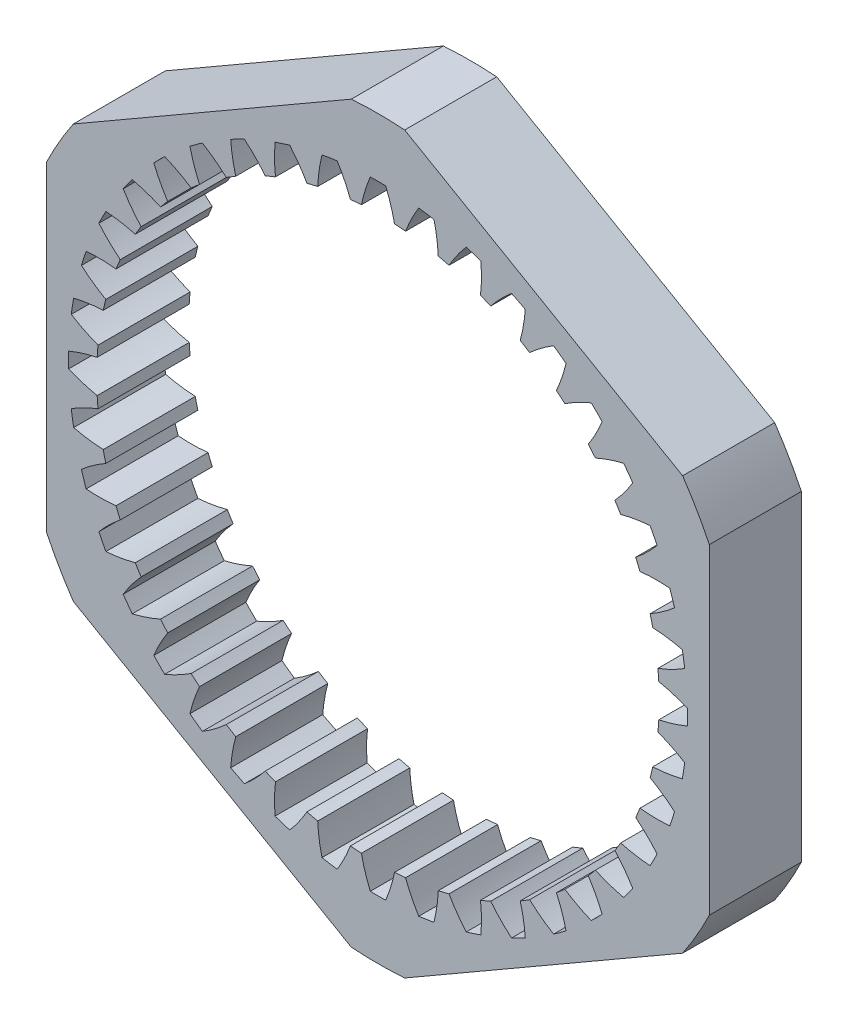
SolidWorks part; units mm, degrees
material "AISI 4130 Steel, annealed at 865C"
ref_plane "Front Plane" through (0, 0, 0) normal (0, 0, 1) x (1, 0, 0)
ref_plane "Top Plane" through (0, 0, 0) normal (0, 1, 0) x (1, 0, 0)
ref_plane "Right Plane" through (0, 0, 0) normal (1, 0, 0) x (0, 0, -1)
ref_plane "Plane1" through (0, 0, -7.9375) normal (0, 0, -1) x (-1, 0, 0)
sketch "Sketch1" plane through (0, 0, -7.9375) normal (0, 0, -1) x (-1, 0, 0)
  line L0 (-28.575, 13.8395) -> (-28.575, -13.8395)
  line L1 (-26.2729, -17.8269) -> (-2.3021, -31.6664)
  line L2 (2.3021, -31.6664) -> (26.2729, -17.8269)
  line L3 (28.575, -13.8395) -> (28.575, 13.8395)
  line L4 (26.2729, 17.8269) -> (2.3021, 31.6664)
  line L5 (-2.3021, 31.6664) -> (-26.2729, 17.8269)
  arc A0 (-26.2729, 17.8269) -> (-28.575, 13.8395) centre (0, 0) ccw
  arc A1 (-28.575, -13.8395) -> (-26.2729, -17.8269) centre (0, 0) ccw
  arc A2 (-2.3021, -31.6664) -> (2.3021, -31.6664) centre (0, 0) ccw
  arc A3 (26.2729, -17.8269) -> (28.575, -13.8395) centre (0, 0) ccw
  arc A4 (28.575, 13.8395) -> (26.2729, 17.8269) centre (0, 0) ccw
  arc A5 (2.3021, 31.6664) -> (-2.3021, 31.6664) centre (0, 0) ccw
  arc A6 (8.841, -22.5885) -> (8.8744, -25.1637) centre (-4.34, -24.0476) cw
  arc A7 (8.8744, -25.1637) -> (7.6113, -25.5741) centre (0, 0) cw
  arc A8 (7.6113, -25.5741) -> (6.1247, -23.4711) centre (17.6459, -16.9039) cw
  arc A9 (6.1247, -23.4711) -> (5.1985, -23.6934) centre (0, 0) cw
  arc A10 (5.1985, -23.6934) -> (4.8287, -26.2421) centre (-8.0484, -23.0726) cw
  arc A11 (4.8287, -26.2421) -> (3.5169, -26.4499) centre (0, 0) cw
  arc A12 (3.5169, -26.4499) -> (2.3776, -24.1402) centre (14.7843, -19.4562) cw
  arc A13 (2.3776, -24.1402) -> (1.428, -24.2149) centre (0, 0) cw
  arc A14 (1.428, -24.2149) -> (0.6641, -26.6744) centre (-11.5587, -21.5295) cw
  arc A15 (0.6641, -26.6744) -> (-0.6641, -26.6744) centre (0, 0) cw
  arc A16 (-0.6641, -26.6744) -> (-1.428, -24.2149) centre (11.5587, -21.5295) cw
  arc A17 (-1.428, -24.2149) -> (-2.3776, -24.1402) centre (0, 0) cw
  arc A18 (-2.3776, -24.1402) -> (-3.5169, -26.4499) centre (-14.7843, -19.4562) cw
  arc A19 (-3.5169, -26.4499) -> (-4.8287, -26.2421) centre (0, 0) cw
  arc A20 (-4.8287, -26.2421) -> (-5.1985, -23.6934) centre (8.0484, -23.0726) cw
  arc A21 (-5.1985, -23.6934) -> (-6.1247, -23.4711) centre (0, 0) cw
  arc A22 (-6.1247, -23.4711) -> (-7.6113, -25.5741) centre (-17.6459, -16.9039) cw
  arc A23 (-7.6113, -25.5741) -> (-8.8744, -25.1637) centre (0, 0) cw
  arc A24 (-8.8744, -25.1637) -> (-8.841, -22.5885) centre (4.34, -24.0476) cw
  arc A25 (-8.841, -22.5885) -> (-9.721, -22.224) centre (0, 0) cw
  arc A26 (-9.721, -22.224) -> (-11.5183, -24.0686) centre (-20.073, -13.9353) cw
  arc A27 (-11.5183, -24.0686) -> (-12.7016, -23.4656) centre (0, 0) cw
  arc A28 (-12.7016, -23.4656) -> (-12.2657, -20.9273) centre (0.5247, -24.4304) cw
  arc A29 (-12.2657, -20.9273) -> (-13.0779, -20.4297) centre (0, 0) cw
  arc A30 (-13.0779, -20.4297) -> (-15.1416, -21.9704) centre (-22.0059, -10.6237) cw
  arc A31 (-15.1416, -21.9704) -> (-16.2161, -21.1897) centre (0, 0) cw
  arc A32 (-16.2161, -21.1897) -> (-15.3885, -18.7509) centre (-3.3035, -24.2117) cw
  arc A33 (-15.3885, -18.7509) -> (-16.1128, -18.1323) centre (0, 0) cw
  arc A34 (-16.1128, -18.1323) -> (-18.3921, -19.3312) centre (-23.3969, -7.0504) cw
  arc A35 (-18.3921, -19.3312) -> (-19.3312, -18.3921) centre (0, 0) cw
  arc A36 (-19.3312, -18.3921) -> (-18.1323, -16.1128) centre (-7.0504, -23.3969) cw
  arc A37 (-18.1323, -16.1128) -> (-18.7509, -15.3885) centre (0, 0) cw
  arc A38 (-18.7509, -15.3885) -> (-21.1897, -16.2161) centre (-24.2117, -3.3035) cw
  arc A39 (-21.1897, -16.2161) -> (-21.9704, -15.1416) centre (0, 0) cw
  arc A40 (-21.9704, -15.1416) -> (-20.4297, -13.0779) centre (-10.6237, -22.0059) cw
  arc A41 (-20.4297, -13.0779) -> (-20.9273, -12.2657) centre (0, 0) cw
  arc A42 (-20.9273, -12.2657) -> (-23.4656, -12.7016) centre (-24.4304, 0.5247) cw
  arc A43 (-23.4656, -12.7016) -> (-24.0686, -11.5183) centre (0, 0) cw
  arc A44 (-24.0686, -11.5183) -> (-22.224, -9.721) centre (-13.9353, -20.073) cw
  arc A45 (-22.224, -9.721) -> (-22.5885, -8.841) centre (0, 0) cw
  arc A46 (-22.5885, -8.841) -> (-25.1637, -8.8744) centre (-24.0476, 4.34) cw
  arc A47 (-25.1637, -8.8744) -> (-25.5741, -7.6113) centre (0, 0) cw
  arc A48 (-25.5741, -7.6113) -> (-23.4711, -6.1247) centre (-16.9039, -17.6459) cw
  arc A49 (-23.4711, -6.1247) -> (-23.6934, -5.1985) centre (0, 0) cw
  arc A50 (-23.6934, -5.1985) -> (-26.2421, -4.8287) centre (-23.0726, 8.0484) cw
  arc A51 (-26.2421, -4.8287) -> (-26.4499, -3.5169) centre (0, 0) cw
  arc A52 (-26.4499, -3.5169) -> (-24.1402, -2.3776) centre (-19.4562, -14.7843) cw
  arc A53 (-24.1402, -2.3776) -> (-24.2149, -1.428) centre (0, 0) cw
  arc A54 (-24.2149, -1.428) -> (-26.6744, -0.6641) centre (-21.5295, 11.5587) cw
  arc A55 (-26.6744, -0.6641) -> (-26.6744, 0.6641) centre (0, 0) cw
  arc A56 (-26.6744, 0.6641) -> (-24.2149, 1.428) centre (-21.5295, -11.5587) cw
  arc A57 (-24.2149, 1.428) -> (-24.1402, 2.3776) centre (0, 0) cw
  arc A58 (-24.1402, 2.3776) -> (-26.4499, 3.5169) centre (-19.4562, 14.7843) cw
  arc A59 (-26.4499, 3.5169) -> (-26.2421, 4.8287) centre (0, 0) cw
  arc A60 (-26.2421, 4.8287) -> (-23.6934, 5.1985) centre (-23.0726, -8.0484) cw
  arc A61 (-23.6934, 5.1985) -> (-23.4711, 6.1247) centre (0, 0) cw
  arc A62 (-23.4711, 6.1247) -> (-25.5741, 7.6113) centre (-16.9039, 17.6459) cw
  arc A63 (-25.5741, 7.6113) -> (-25.1637, 8.8744) centre (0, 0) cw
  arc A64 (-25.1637, 8.8744) -> (-22.5885, 8.841) centre (-24.0476, -4.34) cw
  arc A65 (-22.5885, 8.841) -> (-22.224, 9.721) centre (0, 0) cw
  arc A66 (-22.224, 9.721) -> (-24.0686, 11.5183) centre (-13.9353, 20.073) cw
  arc A67 (-24.0686, 11.5183) -> (-23.4656, 12.7016) centre (0, 0) cw
  arc A68 (-23.4656, 12.7016) -> (-20.9273, 12.2657) centre (-24.4304, -0.5247) cw
  arc A69 (-20.9273, 12.2657) -> (-20.4297, 13.0779) centre (0, 0) cw
  arc A70 (-20.4297, 13.0779) -> (-21.9704, 15.1416) centre (-10.6237, 22.0059) cw
  arc A71 (-21.9704, 15.1416) -> (-21.1897, 16.2161) centre (0, 0) cw
  arc A72 (-21.1897, 16.2161) -> (-18.7509, 15.3885) centre (-24.2117, 3.3035) cw
  arc A73 (-18.7509, 15.3885) -> (-18.1323, 16.1128) centre (0, 0) cw
  arc A74 (-18.1323, 16.1128) -> (-19.3312, 18.3921) centre (-7.0504, 23.3969) cw
  arc A75 (-19.3312, 18.3921) -> (-18.3921, 19.3312) centre (0, 0) cw
  arc A76 (-18.3921, 19.3312) -> (-16.1128, 18.1323) centre (-23.3969, 7.0504) cw
  arc A77 (-16.1128, 18.1323) -> (-15.3885, 18.7509) centre (0, 0) cw
  arc A78 (-15.3885, 18.7509) -> (-16.2161, 21.1897) centre (-3.3035, 24.2117) cw
  arc A79 (-16.2161, 21.1897) -> (-15.1416, 21.9704) centre (0, 0) cw
  arc A80 (-15.1416, 21.9704) -> (-13.0779, 20.4297) centre (-22.0059, 10.6237) cw
  arc A81 (-13.0779, 20.4297) -> (-12.2657, 20.9273) centre (0, 0) cw
  arc A82 (-12.2657, 20.9273) -> (-12.7016, 23.4656) centre (0.5247, 24.4304) cw
  arc A83 (-12.7016, 23.4656) -> (-11.5183, 24.0686) centre (0, 0) cw
  arc A84 (-11.5183, 24.0686) -> (-9.721, 22.224) centre (-20.073, 13.9353) cw
  arc A85 (-9.721, 22.224) -> (-8.841, 22.5885) centre (0, 0) cw
  arc A86 (-8.841, 22.5885) -> (-8.8744, 25.1637) centre (4.34, 24.0476) cw
  arc A87 (-8.8744, 25.1637) -> (-7.6113, 25.5741) centre (0, 0) cw
  arc A88 (-7.6113, 25.5741) -> (-6.1247, 23.4711) centre (-17.6459, 16.9039) cw
  arc A89 (-6.1247, 23.4711) -> (-5.1985, 23.6934) centre (0, 0) cw
  arc A90 (-5.1985, 23.6934) -> (-4.8287, 26.2421) centre (8.0484, 23.0726) cw
  arc A91 (-4.8287, 26.2421) -> (-3.5169, 26.4499) centre (0, 0) cw
  arc A92 (-3.5169, 26.4499) -> (-2.3776, 24.1402) centre (-14.7843, 19.4562) cw
  arc A93 (-2.3776, 24.1402) -> (-1.428, 24.2149) centre (0, 0) cw
  arc A94 (-1.428, 24.2149) -> (-0.6641, 26.6744) centre (11.5587, 21.5295) cw
  arc A95 (-0.6641, 26.6744) -> (0.6641, 26.6744) centre (0, 0) cw
  arc A96 (0.6641, 26.6744) -> (1.428, 24.2149) centre (-11.5587, 21.5295) cw
  arc A97 (1.428, 24.2149) -> (2.3776, 24.1402) centre (0, 0) cw
  arc A98 (2.3776, 24.1402) -> (3.5169, 26.4499) centre (14.7843, 19.4562) cw
  arc A99 (3.5169, 26.4499) -> (4.8287, 26.2421) centre (0, 0) cw
  arc A100 (4.8287, 26.2421) -> (5.1985, 23.6934) centre (-8.0484, 23.0726) cw
  arc A101 (5.1985, 23.6934) -> (6.1247, 23.4711) centre (0, 0) cw
  arc A102 (6.1247, 23.4711) -> (7.6113, 25.5741) centre (17.6459, 16.9039) cw
  arc A103 (7.6113, 25.5741) -> (8.8744, 25.1637) centre (0, 0) cw
  arc A104 (8.8744, 25.1637) -> (8.841, 22.5885) centre (-4.34, 24.0476) cw
  arc A105 (8.841, 22.5885) -> (9.721, 22.224) centre (0, 0) cw
  arc A106 (9.721, 22.224) -> (11.5183, 24.0686) centre (20.073, 13.9353) cw
  arc A107 (11.5183, 24.0686) -> (12.7016, 23.4656) centre (0, 0) cw
  arc A108 (12.7016, 23.4656) -> (12.2657, 20.9273) centre (-0.5247, 24.4304) cw
  arc A109 (12.2657, 20.9273) -> (13.0779, 20.4297) centre (0, 0) cw
  arc A110 (13.0779, 20.4297) -> (15.1416, 21.9704) centre (22.0059, 10.6237) cw
  arc A111 (15.1416, 21.9704) -> (16.2161, 21.1897) centre (0, 0) cw
  arc A112 (16.2161, 21.1897) -> (15.3885, 18.7509) centre (3.3035, 24.2117) cw
  arc A113 (15.3885, 18.7509) -> (16.1128, 18.1323) centre (0, 0) cw
  arc A114 (16.1128, 18.1323) -> (18.3921, 19.3312) centre (23.3969, 7.0504) cw
  arc A115 (18.3921, 19.3312) -> (19.3312, 18.3921) centre (0, 0) cw
  arc A116 (19.3312, 18.3921) -> (18.1323, 16.1128) centre (7.0504, 23.3969) cw
  arc A117 (18.1323, 16.1128) -> (18.7509, 15.3885) centre (0, 0) cw
  arc A118 (18.7509, 15.3885) -> (21.1897, 16.2161) centre (24.2117, 3.3035) cw
  arc A119 (21.1897, 16.2161) -> (21.9704, 15.1416) centre (0, 0) cw
  arc A120 (21.9704, 15.1416) -> (20.4297, 13.0779) centre (10.6237, 22.0059) cw
  arc A121 (20.4297, 13.0779) -> (20.9273, 12.2657) centre (0, 0) cw
  arc A122 (20.9273, 12.2657) -> (23.4656, 12.7016) centre (24.4304, -0.5247) cw
  arc A123 (23.4656, 12.7016) -> (24.0686, 11.5183) centre (0, 0) cw
  arc A124 (24.0686, 11.5183) -> (22.224, 9.721) centre (13.9353, 20.073) cw
  arc A125 (22.224, 9.721) -> (22.5885, 8.841) centre (0, 0) cw
  arc A126 (22.5885, 8.841) -> (25.1637, 8.8744) centre (24.0476, -4.34) cw
  arc A127 (25.1637, 8.8744) -> (25.5741, 7.6113) centre (0, 0) cw
  arc A128 (25.5741, 7.6113) -> (23.4711, 6.1247) centre (16.9039, 17.6459) cw
  arc A129 (23.4711, 6.1247) -> (23.6934, 5.1985) centre (0, 0) cw
  arc A130 (23.6934, 5.1985) -> (26.2421, 4.8287) centre (23.0726, -8.0484) cw
  arc A131 (26.2421, 4.8287) -> (26.4499, 3.5169) centre (0, 0) cw
  arc A132 (26.4499, 3.5169) -> (24.1402, 2.3776) centre (19.4562, 14.7843) cw
  arc A133 (24.1402, 2.3776) -> (24.2149, 1.428) centre (0, 0) cw
  arc A134 (24.2149, 1.428) -> (26.6744, 0.6641) centre (21.5295, -11.5587) cw
  arc A135 (26.6744, 0.6641) -> (26.6744, -0.6641) centre (0, 0) cw
  arc A136 (26.6744, -0.6641) -> (24.2149, -1.428) centre (21.5295, 11.5587) cw
  arc A137 (24.2149, -1.428) -> (24.1402, -2.3776) centre (0, 0) cw
  arc A138 (24.1402, -2.3776) -> (26.4499, -3.5169) centre (19.4562, -14.7843) cw
  arc A139 (26.4499, -3.5169) -> (26.2421, -4.8287) centre (0, 0) cw
  arc A140 (26.2421, -4.8287) -> (23.6934, -5.1985) centre (23.0726, 8.0484) cw
  arc A141 (23.6934, -5.1985) -> (23.4711, -6.1247) centre (0, 0) cw
  arc A142 (23.4711, -6.1247) -> (25.5741, -7.6113) centre (16.9039, -17.6459) cw
  arc A143 (25.5741, -7.6113) -> (25.1637, -8.8744) centre (0, 0) cw
  arc A144 (25.1637, -8.8744) -> (22.5885, -8.841) centre (24.0476, 4.34) cw
  arc A145 (22.5885, -8.841) -> (22.224, -9.721) centre (0, 0) cw
  arc A146 (22.224, -9.721) -> (24.0686, -11.5183) centre (13.9353, -20.073) cw
  arc A147 (24.0686, -11.5183) -> (23.4656, -12.7016) centre (0, 0) cw
  arc A148 (23.4656, -12.7016) -> (20.9273, -12.2657) centre (24.4304, 0.5247) cw
  arc A149 (20.9273, -12.2657) -> (20.4297, -13.0779) centre (0, 0) cw
  arc A150 (20.4297, -13.0779) -> (21.9704, -15.1416) centre (10.6237, -22.0059) cw
  arc A151 (21.9704, -15.1416) -> (21.1897, -16.2161) centre (0, 0) cw
  arc A152 (21.1897, -16.2161) -> (18.7509, -15.3885) centre (24.2117, -3.3035) cw
  arc A153 (18.7509, -15.3885) -> (18.1323, -16.1128) centre (0, 0) cw
  arc A154 (18.1323, -16.1128) -> (19.3312, -18.3921) centre (7.0504, -23.3969) cw
  arc A155 (19.3312, -18.3921) -> (18.3921, -19.3312) centre (0, 0) cw
  arc A156 (18.3921, -19.3312) -> (16.1128, -18.1323) centre (23.3969, -7.0504) cw
  arc A157 (16.1128, -18.1323) -> (15.3885, -18.7509) centre (0, 0) cw
  arc A158 (15.3885, -18.7509) -> (16.2161, -21.1897) centre (3.3035, -24.2117) cw
  arc A159 (16.2161, -21.1897) -> (15.1416, -21.9704) centre (0, 0) cw
  arc A160 (15.1416, -21.9704) -> (13.0779, -20.4297) centre (22.0059, -10.6237) cw
  arc A161 (13.0779, -20.4297) -> (12.2657, -20.9273) centre (0, 0) cw
  arc A162 (12.2657, -20.9273) -> (12.7016, -23.4656) centre (-0.5247, -24.4304) cw
  arc A163 (12.7016, -23.4656) -> (11.5183, -24.0686) centre (0, 0) cw
  arc A164 (11.5183, -24.0686) -> (9.721, -22.224) centre (20.073, -13.9353) cw
  arc A165 (9.721, -22.224) -> (8.841, -22.5885) centre (0, 0) cw
extrude "Boss-Extrude1" add sketch "Sketch1" against normal blind 7.9375
